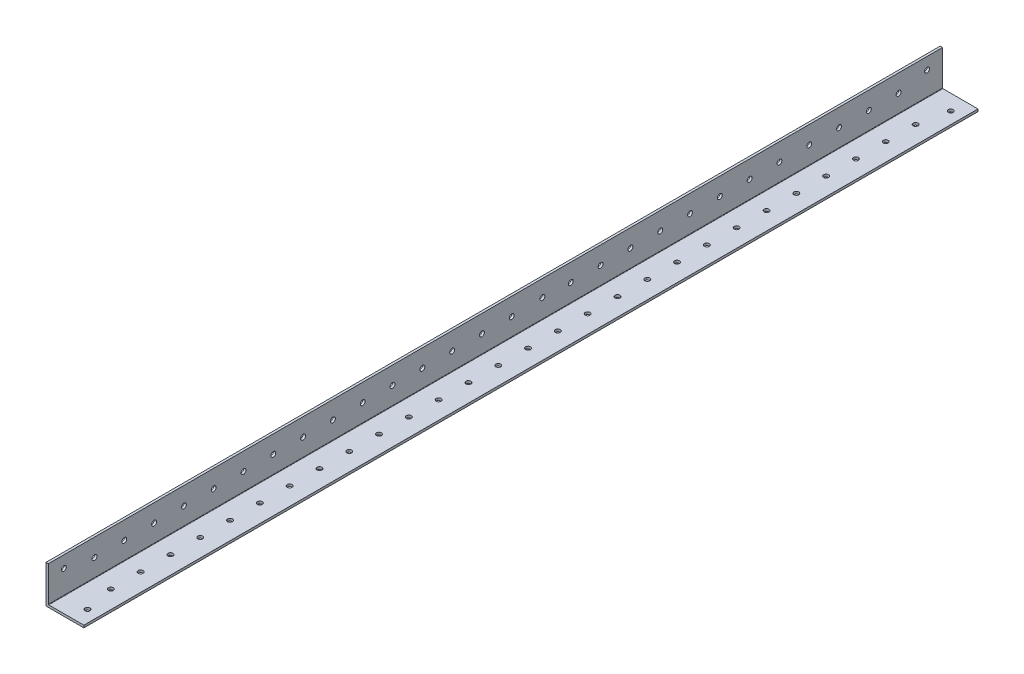
SolidWorks part; units mm, degrees
material "6061 Alloy"
ref_plane "Front Plane" through (0, 0, 0) normal (0, 0, 1) x (1, 0, 0)
ref_plane "Top Plane" through (0, 0, 0) normal (0, 1, 0) x (1, 0, 0)
ref_plane "Right Plane" through (0, 0, 0) normal (1, 0, 0) x (0, 0, -1)
sketch "Sketch1" plane through (0, 0, 0) normal (0, 0, 1) x (1, 0, 0)
  line L0 (0, 25.4) -> (0, 0) construction
  line L1 (0, 0) -> (25.4, 0) construction
  line L2 (25.4, 0) -> (25.4, 1.5875) construction
  line L3 (25.4, 1.5875) -> (1.5875, 1.5875) construction
  line L4 (1.5875, 1.5875) -> (1.5875, 25.4) construction
  line L6 (1.5875, 25.4) -> (0, 25.4) construction
  arc A0 (1.5875, 1.8415) -> (1.8415, 1.5875) centre (1.8415, 1.8415) ccw construction
  point P4 (0, 0)
  dimension "Inside Corner Radius" = 0.254
  dimension "Outside Height" = 25.4
  dimension "Inside Height" = 23.8125
  dimension "Outside Width" = 25.4
  dimension "Inside Width" = 23.8125
  dimension "Wall Thickness" = 1.5875
  dimension "Shape" = 90
sketch "Sketch2" plane through (0, 0, 0) normal (1, 0, 0) x (0, 0, -1)
  line L0 (1219.2, 0) -> (-1219.2, 0) construction
  line L1 (-1219.2, 25.4) -> (-1219.2, 0) construction
  line L2 (1219.2, 25.4) -> (1219.2, 0) construction
  point P0 (-1189.99, 0)
  point P4 (0, 0)
  point P6 (1189.99, 0)
  dimension "D1" = 29.21
  dimension "D2" = 29.21
  dimension "D3" = 25.4
  dimension "Length" = 2438.4
sketch "Sketch3" plane through (0, 0, 0) normal (0, 0, 1) x (1, 0, 0)
  line L0 (1.5875, 25.4) -> (0, 25.4)
  line L1 (0, 25.4) -> (0, 0)
  line L2 (0, 0) -> (25.4, 0)
  line L3 (25.4, 0) -> (25.4, 1.5875)
  line L4 (25.4, 1.5875) -> (1.5875, 1.5875)
  line L5 (1.5875, 1.5875) -> (1.5875, 25.4)
extrude "Boss-Extrude1" add sketch "Sketch3" along normal mid plane 2438.4
fillet "Fillet1" radius 0.254 1 edges at (1.5875, 1.5875, 0)
sketch "Sketch4" plane through (0, 0, 0) normal (-1, 0, 0) x (0, 0, 1)
  line L0 (1219.2, 25.4) -> (1219.2, 0) construction
  line L1 (-1219.2, 0) -> (619.2, 0)
  line L2 (-1219.2, 0) -> (-1219.2, 74.9453)
  line L3 (-1219.2, 74.9453) -> (619.2, 74.9453)
  line L4 (619.2, 0) -> (619.2, 74.9453)
  dimension "D1" = 600
extrude "Cut-Extrude1" cut sketch "Sketch4" against normal blind 60
sketch "Sketch5" plane through (0, 1.5875, 0) normal (0, 1, 0) x (1, 0, 0)
  line L0 (17.4625, -1208.8241) -> (17.4625, -1189.2) construction
  line L1 (13.4937, -649.2) -> (13.4937, -629.5759) construction
  line L3 (1.5875, -1189.2) -> (25.4, -1189.2) construction
  line L4 (1.5875, -1219.2) -> (1.5875, -619.2) construction
  line L5 (25.4, -1219.2) -> (25.4, -619.2) construction
  line L6 (13.4937, -629.5759) -> (17.4625, -629.5759) construction
  line L7 (17.4625, -629.5759) -> (13.4937, -629.5759) construction
  circle A30 centre (17.4625, -629.5759) radius 1.65
  circle A31 centre (17.4625, -1208.8241) radius 1.65
  circle A32 centre (13.4938, -1189.2) radius 1.65
  circle A33 centre (13.4938, -1169.2) radius 1.65
  circle A34 centre (13.4938, -1149.2) radius 1.65
  circle A35 centre (13.4938, -1129.2) radius 1.65
  circle A36 centre (13.4938, -1109.2) radius 1.65
  circle A37 centre (13.4938, -1089.2) radius 1.65
  circle A38 centre (13.4938, -1069.2) radius 1.65
  circle A39 centre (13.4938, -1049.2) radius 1.65
  circle A40 centre (13.4938, -1029.2) radius 1.65
  circle A41 centre (13.4938, -1009.2) radius 1.65
  circle A42 centre (13.4938, -989.2) radius 1.65
  circle A43 centre (13.4938, -969.2) radius 1.65
  circle A44 centre (13.4938, -949.2) radius 1.65
  circle A45 centre (13.4938, -929.2) radius 1.65
  circle A46 centre (13.4938, -909.2) radius 1.65
  circle A47 centre (13.4938, -889.2) radius 1.65
  circle A48 centre (13.4938, -869.2) radius 1.65
  circle A49 centre (13.4938, -849.2) radius 1.65
  circle A50 centre (13.4938, -829.2) radius 1.65
  circle A51 centre (13.4938, -809.2) radius 1.65
  circle A52 centre (13.4938, -789.2) radius 1.65
  circle A53 centre (13.4938, -769.2) radius 1.65
  circle A54 centre (13.4938, -749.2) radius 1.65
  circle A55 centre (13.4938, -729.2) radius 1.65
  circle A56 centre (13.4938, -709.2) radius 1.65
  circle A57 centre (13.4938, -689.2) radius 1.65
  circle A58 centre (13.4938, -669.2) radius 1.65
  circle A59 centre (13.4937, -649.2) radius 1.65
  dimension "D1" = 3.3
  dimension "D2" = 3.3
  dimension "D3" = 28
  dimension "D4" = 20
extrude "Cut-Extrude2" cut sketch "Sketch5" against normal blind 10
sketch "Sketch9" plane through (1.5875, 0, 0) normal (1, 0, 0) x (0, 0, -1)
  line L0 (-648.6348, 1.5875) -> (-648.6348, 25.4) construction
  line L1 (-1219.2, 1.5875) -> (-619.2, 1.5875) construction
  line L2 (-1219.2, 25.4) -> (-619.2, 25.4) construction
  line L3 (-629.5759, 17.4625) -> (-648.6348, 17.4625) construction
  line L4 (-634.3937, -3.175) -> (-630.9937, -3.175) construction
  line L5 (-634.3937, 0) -> (-634.3937, -6.35) construction
  line L6 (-630.9937, -6.35) -> (-630.9937, 0) construction
  line L7 (-632.6937, -3.175) -> (-887.6937, -3.175) construction
  line L8 (-887.6937, -3.175) -> (-887.6937, 25.4) construction
  line L9 (-868.6348, 13.4937) -> (-887.6937, 13.4937) construction
  line L10 (-908.2589, 1.5875) -> (-908.2589, 25.4) construction
  line L11 (-908.2589, 10.4618) -> (-887.6937, 10.4618) construction
  line L12 (-1208.8241, 17.463) -> (-1208.8241, 3.8191) construction
  line L13 (-1215.3265, 3.8191) -> (-1204.9125, 3.8191) construction
  line L14 (-1188.2589, 13.4937) -> (-1208.8241, 13.4937) construction
  circle A0 centre (-629.5759, 17.4625) radius 1.65
  circle A1 centre (-648.6348, 13.4938) radius 1.65
  circle A2 centre (-887.6937, 14.2875) radius 1.65
  circle A3 centre (-1208.8241, 17.463) radius 1.65
  circle A4 centre (-668.6348, 13.4938) radius 1.65
  circle A5 centre (-688.6348, 13.4938) radius 1.65
  circle A6 centre (-708.6348, 13.4938) radius 1.65
  circle A7 centre (-728.6348, 13.4938) radius 1.65
  circle A8 centre (-748.6348, 13.4938) radius 1.65
  circle A9 centre (-768.6348, 13.4938) radius 1.65
  circle A10 centre (-788.6348, 13.4938) radius 1.65
  circle A11 centre (-808.6348, 13.4938) radius 1.65
  circle A12 centre (-828.6348, 13.4938) radius 1.65
  circle A13 centre (-848.6348, 13.4938) radius 1.65
  circle A14 centre (-868.6348, 13.4937) radius 1.65
  circle A16 centre (-888.6348, 13.4937) radius 1.65 [skipped]
  circle A17 centre (-908.2589, 13.4938) radius 1.65
  circle A18 centre (-928.2589, 13.4938) radius 1.65
  circle A19 centre (-948.2589, 13.4938) radius 1.65
  circle A20 centre (-968.2589, 13.4938) radius 1.65
  circle A21 centre (-988.2589, 13.4938) radius 1.65
  circle A22 centre (-1008.2589, 13.4938) radius 1.65
  circle A23 centre (-1028.2589, 13.4938) radius 1.65
  circle A24 centre (-1048.2589, 13.4938) radius 1.65
  circle A25 centre (-1068.2589, 13.4938) radius 1.65
  circle A26 centre (-1088.2589, 13.4938) radius 1.65
  circle A27 centre (-1108.2589, 13.4938) radius 1.65
  circle A28 centre (-1128.2589, 13.4938) radius 1.65
  circle A29 centre (-1148.2589, 13.4938) radius 1.65
  circle A30 centre (-1168.2589, 13.4938) radius 1.65
  circle A31 centre (-1188.2589, 13.4937) radius 1.65
  dimension "D1" = 12.7
  dimension "D3" = 3.3
  dimension "D2" = 255
  dimension "D5" = 20
  dimension "D6" = 20
  dimension "D4" = 13
extrude "Cut-Extrude6" cut sketch "Sketch9" against normal blind 60
equation "\"D1@Boss-Extrude1\"=\"Length@Sketch2\""
equation "\"D1@Sketch2\" = \"Outside Width@Sketch1\" * 1.15"
equation "\"D2@Sketch2\"=\"D1@Sketch2\""
equation "\"D1@Fillet1\"=\"Inside Corner Radius@Sketch1\""
equation "\"D3@Sketch2\"=\"Outside Height@Sketch1\""
